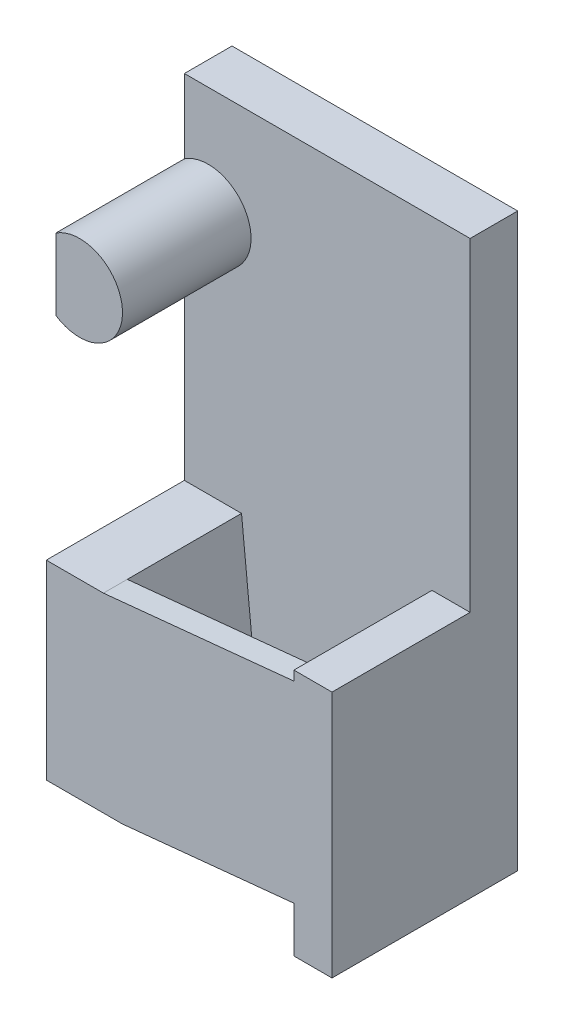
SolidWorks part; units mm, degrees
ref_plane "Front Plane" through (0, 0, 0) normal (0, 0, 1) x (1, 0, 0)
ref_plane "Top Plane" through (0, 0, 0) normal (0, 1, 0) x (1, 0, 0)
ref_plane "Right Plane" through (0, 0, 0) normal (1, 0, 0) x (0, 0, -1)
sketch "Sketch1" plane through (0, 0, 0) normal (0, 0, 1) x (1, 0, 0)
  line L1 (0, 0) -> (60, 0)
  line L2 (0, 0) -> (0, 120)
  line L3 (0, 120) -> (60, 120)
  line L4 (60, 0) -> (60, 120)
extrude "Boss-Extrude1" add sketch "Sketch1" along normal blind 10
sketch "Sketch2" plane through (0, 0, 10) normal (0, 0, 1) x (1, 0, 0)
  line L1 (60, 0) -> (52, 0)
  line L2 (60, 0) -> (60, 52)
  line L3 (60, 52) -> (52, 52)
  line L4 (52, 0) -> (52, 52)
sketch "Sketch3" plane through (0, 0, 10) normal (0, 0, 1) x (1, 0, 0)
  circle A0 centre (5, 97) radius 9
extrude "Boss-Extrude3" add sketch "Sketch3" along normal blind 27
sketch "Sketch4" plane through (0, 0, 37) normal (0, 0, 1) x (1, 0, 0)
  line L0 (0, 104.4833) -> (0, 89.5167)
  line L1 (0, 89.5167) -> (-21.0754, 89.5167)
  line L2 (-21.0754, 89.5167) -> (-21.0754, 106.9983)
  line L3 (-21.0754, 106.9983) -> (0, 104.4833)
extrude "Cut-Extrude1" cut sketch "Sketch4" against normal through all
sketch "Sketch5" plane through (0, 0, 10) normal (0, 0, 1) x (1, 0, 0)
  line L0 (0, 89.5167) -> (0, 0) construction
  line L1 (16, 6) -> (0, 6)
  line L2 (16, 6) -> (16, 46)
  line L3 (16, 46) -> (0, 46)
  line L4 (0, 6) -> (0, 46)
extrude "Boss-Extrude4" add sketch "Sketch5" along normal blind 29
extrude "Boss-Extrude5" add sketch "Sketch2" along normal blind 29
sketch "Sketch8" plane through (0, 0, 39) normal (0, 0, 1) x (1, 0, 0)
  line L0 (16, 46) -> (12, 46)
  line L1 (16, 46) -> (0, 46) construction
  line L2 (12, 46) -> (16, 6)
  line L3 (16, 6) -> (16, 46)
extrude "Cut-Extrude2" cut sketch "Sketch8" against normal blind 29
sketch "Sketch9" plane through (16.4356, 1.6436, 0) normal (0.995, 0.0995, 0) x (0, 0, -1)
  line L0 (-39, 4.3782) -> (-10, 4.3782) construction
  line L1 (-39, 44.5777) -> (-34, 44.5777)
  line L2 (-39, 44.5777) -> (-39, 4.3782)
  line L3 (-39, 4.3782) -> (-34, 4.3782)
  line L4 (-34, 44.5777) -> (-34, 4.3782)
extrude "Boss-Extrude6" add sketch "Sketch9" along normal blind 42
